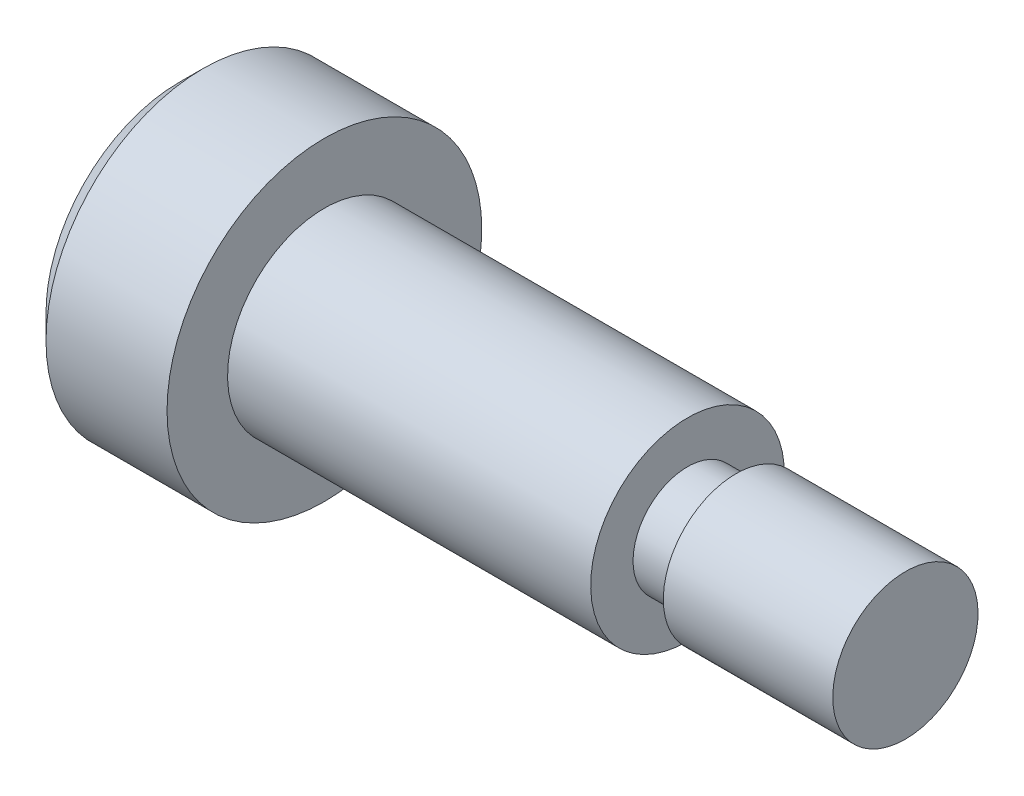
SolidWorks part; units mm, degrees
material "AISI 304"
ref_plane "Front Plane" through (0, 0, 0) normal (0, 0, 1) x (1, 0, 0)
ref_plane "Top Plane" through (0, 0, 0) normal (0, 1, 0) x (1, 0, 0)
ref_plane "Right Plane" through (0, 0, 0) normal (1, 0, 0) x (0, 0, -1)
sketch "Sketch1" plane through (0, 0, 0) normal (0, 0, 1) x (1, 0, 0)
  line L0 (-6, 0) -> (-6, 6.5)
  line L1 (-6, 6.5) -> (0, 6.5)
  line L2 (0, 6.5) -> (0, 4)
  line L3 (0, 4) -> (15, 4)
  line L4 (15, 4) -> (15, 2.25)
  line L5 (15, 2.25) -> (17, 2.25)
  line L6 (17, 2.25) -> (17, 3)
  line L7 (17, 3) -> (24, 3)
  line L8 (24, 3) -> (24, 0)
  line L9 (24, 0) -> (-6, 0)
  line L10 (-26.0126, 0) -> (49.4761, 0) construction
  dimension "D1" = 6
  dimension "D2" = 8
  dimension "D3" = 4.5
  dimension "D4" = 13
  dimension "D5" = 6
  dimension "D6" = 15
  dimension "D7" = 9
  dimension "D8" = 2
revolve "Revolve1" add sketch "Sketch1" angle 360 about L10
cosmetic thread "Cosmetic Thread1" parameters "D2"=4.891
sketch "Sketch2" plane through (-6, 0, 0) normal (-1, 0, 0) x (0, 0, 1)
  line L0 (0, 0) -> (2.8868, 0) construction
  line L1 (2.8868, 0) -> (1.4434, 2.5)
  line L2 (1.4434, 2.5) -> (-1.4434, 2.5)
  line L3 (-1.4434, 2.5) -> (-2.8868, 0)
  line L4 (-2.8868, 0) -> (-1.4434, -2.5)
  line L5 (-1.4434, -2.5) -> (1.4434, -2.5)
  line L6 (1.4434, -2.5) -> (2.8868, 0)
  circle A0 centre (0, 0) radius 2.5 construction
  dimension "D1" = 5
extrude "Cut-Extrude1" cut sketch "Sketch2" against normal blind 3
chamfer "Chamfer1" distance 1 angle 45 1 edges at (-6, -6.5, 0)
